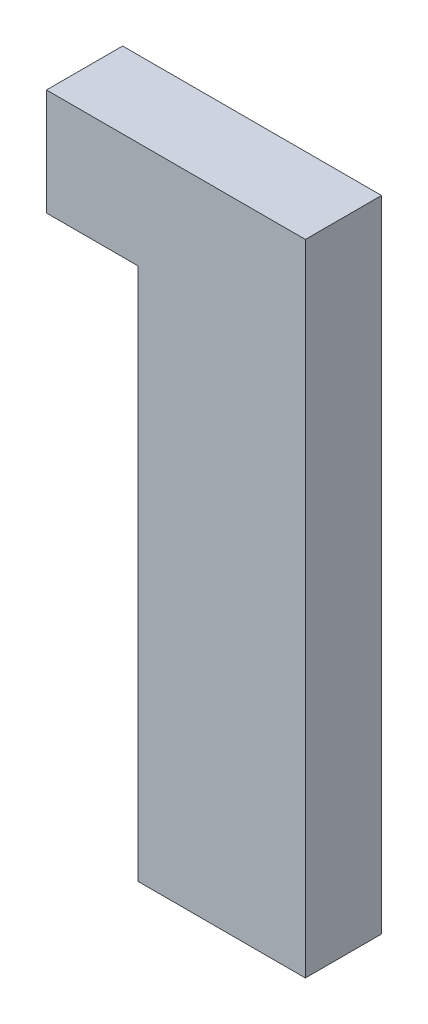
SolidWorks part; units mm, degrees
ref_plane "Front Plane" through (0, 0, 0) normal (0, 0, 1) x (1, 0, 0)
ref_plane "Top Plane" through (0, 0, 0) normal (0, 1, 0) x (1, 0, 0)
ref_plane "Right Plane" through (0, 0, 0) normal (1, 0, 0) x (0, 0, -1)
sketch "Sketch2" plane through (0, 0, 0) normal (0, 0, 1) x (1, 0, 0)
  line L1 (0, 0) -> (-13.97, 0)
  line L2 (0, 0) -> (0, 53.34)
  line L3 (0, 53.34) -> (-13.97, 53.34)
  line L4 (-13.97, 0) -> (-13.97, 53.34)
  line L5 (0, 53.34) -> (-21.59, 53.34)
  line L6 (0, 53.34) -> (0, 44.45)
  line L7 (0, 44.45) -> (-21.59, 44.45)
  line L8 (-21.59, 53.34) -> (-21.59, 44.45)
  dimension "D1" = 13.97
  dimension "D2" = 53.34
  dimension "D3" = 8.89
  dimension "D4" = 21.59
extrude "Boss-Extrude1" add sketch "Sketch2" along normal blind 6.35 contours L5 L8 L7 L4 | L7 L2 L3 L4 | L2 L7 L4 L1
sketch "Sketch3" plane through (0, 0, 0) normal (0, 0, -1) x (-1, 0, 0)
  line L0 (0, 0) -> (13.97, 0) construction
  line L1 (13.97, 0) -> (13.97, 44.45) construction
  circle A0 centre (6.985, 15.24) radius 4.0005
  dimension "D3" = 8.001
  dimension "D1" = 15.24
  dimension "D2" = 6.985
extrude "Cut-Extrude1" cut sketch "Sketch3" against normal blind 2.794
sketch "Sketch4" plane through (0, 0, 0) normal (0, 0, -1) x (-1, 0, 0)
  line L0 (13.97, 0) -> (13.97, 44.45) construction
  line L4 (6.985, 29.718) -> (9.017, 29.718)
  line L5 (9.017, 15.24) -> (9.017, 29.718)
  line L8 (6.985, 29.718) -> (4.953, 29.718)
  line L9 (4.953, 15.24) -> (4.953, 29.718)
  line L10 (4.953, 15.24) -> (4.953, 0.762)
  line L11 (9.017, 15.24) -> (9.017, 0.762)
  line L12 (4.953, 0.762) -> (9.017, 0.762)
  dimension "D1" = 28.956
  dimension "D2" = 4.953
  dimension "D3" = 9.017
extrude "Cut-Extrude2" cut sketch "Sketch4" against normal blind 1.5875
